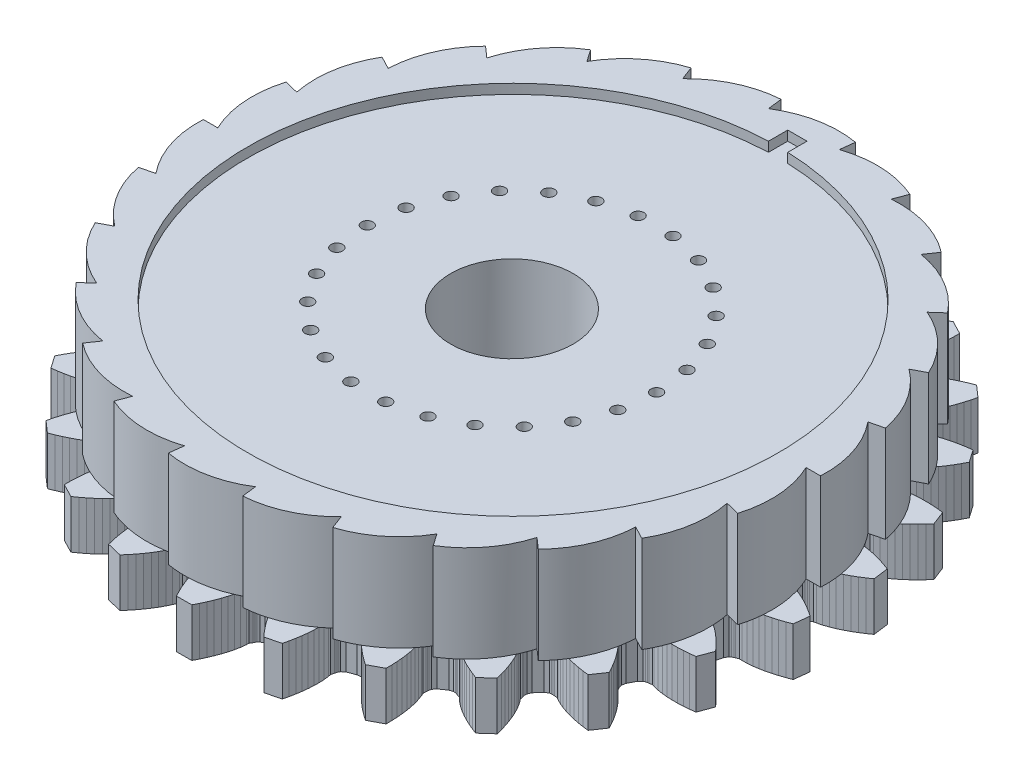
SolidWorks part; units mm, degrees
material "1060 Alloy"
ref_plane "Front Plane" through (0, 0, 0) normal (0, 0, 1) x (1, 0, 0)
ref_plane "Top Plane" through (0, 0, 0) normal (0, 1, 0) x (1, 0, 0)
ref_plane "Right Plane" through (0, 0, 0) normal (1, 0, 0) x (0, 0, -1)
sketch "Sketch1" plane through (0, 0, 0) normal (0, 1, 0) x (1, 0, 0)
  line L0 (0, 0) -> (54.8903, 0) construction
  line L1 (0, 0) -> (47.5263, 11.7142) construction
  line L2 (0, 0) -> (29.6137, 7.2991)
  line L3 (0, 0) -> (32, 0)
  circle A0 centre (0, 0) radius 32 construction
  circle A1 centre (0, 0) radius 30.5 construction
  arc A2 (29.6137, 7.2991) -> (32, 0) centre (21.3514, 0.5583) cw
  circle A3 centre (0, 0) radius 31.25 construction
  dimension "D1" = 62.5
  dimension "D2" = 1.5
  dimension "D4" = 0.75
  dimension "D3" = 13.846
extrude "Extrude ratchet edge" add sketch "Sketch1" along normal blind 10
pattern_circular "Pattern edge to form gear" count 26 over 360 about axis through (0, 0, 0) along (0, 1, 0) of "Extrude ratchet edge"
sketch "Sketch7" plane through (0, 10, 0) normal (0, 1, 0) x (1, 0, 0)
  circle A0 centre (0, 0) radius 6.35
  dimension "D1" = 12.7
sketch "Sketch12" plane through (0, 0, 0) normal (0, -1, 0) x (1, 0, 0)
  line L0 (29.0003, -0.6166) -> (29.1196, -1.0003)
  line L1 (29.1196, -1.0003) -> (29.244, -1.1506)
  line L2 (29.244, -1.1506) -> (29.3694, -1.2597)
  line L3 (29.3694, -1.2597) -> (29.4955, -1.346)
  line L4 (29.4955, -1.346) -> (29.7463, -1.5351)
  line L5 (29.7463, -1.5351) -> (30.0039, -1.5796)
  line L6 (30.0039, -1.5796) -> (30.5166, -1.7122)
  line L7 (30.5166, -1.7122) -> (31.0266, -1.8861)
  line L8 (31.0266, -1.8861) -> (31.5336, -2.0936)
  line L9 (31.5336, -2.0936) -> (32.0376, -2.3308)
  line L10 (32.0376, -2.3308) -> (32.5381, -2.595)
  line L11 (32.5381, -2.595) -> (33.035, -2.8848)
  line L12 (33.035, -2.8848) -> (33.5277, -3.1987)
  line L13 (33.5277, -3.1987) -> (34.0159, -3.5359)
  line L14 (34.0159, -3.5359) -> (33.8164, -5.1042)
  line L15 (33.8164, -5.1042) -> (33.2594, -5.3084)
  line L16 (33.2594, -5.3084) -> (32.7038, -5.4891)
  line L17 (32.7038, -5.4891) -> (32.1503, -5.6453)
  line L18 (32.1503, -5.6453) -> (31.5995, -5.7759)
  line L19 (31.5995, -5.7759) -> (31.0523, -5.8793)
  line L20 (31.0523, -5.8793) -> (30.5094, -5.9534)
  line L21 (30.5094, -5.9534) -> (29.9722, -5.9942)
  line L22 (29.9722, -5.9942) -> (29.4426, -5.9942)
  line L23 (29.4426, -5.9942) -> (29.182, -5.9728)
  line L24 (29.182, -5.9728) -> (28.8919, -6.0931)
  line L25 (28.8919, -6.0931) -> (28.7482, -6.1452)
  line L26 (28.7482, -6.1452) -> (28.5995, -6.2194)
  line L27 (28.5995, -6.2194) -> (28.4414, -6.3338)
  line L28 (28.4414, -6.3338) -> (28.2299, -6.6755)
  line L29 (28.2299, -6.6755) -> (28.0119, -7.539)
  line L30 (28.0119, -7.539) -> (28.0359, -7.9401)
  line L31 (28.0359, -7.9401) -> (28.1207, -8.1159)
  line L32 (28.1207, -8.1159) -> (28.2164, -8.2517)
  line L33 (28.2164, -8.2517) -> (28.3182, -8.3658)
  line L34 (28.3182, -8.3658) -> (28.5164, -8.6094)
  line L35 (28.5164, -8.6094) -> (28.7559, -8.7142)
  line L36 (28.7559, -8.7142) -> (29.222, -8.9657)
  line L37 (29.222, -8.9657) -> (29.6755, -9.2566)
  line L38 (29.6755, -9.2566) -> (30.1181, -9.5794)
  line L39 (30.1181, -9.5794) -> (30.5507, -9.9303)
  line L40 (30.5507, -9.9303) -> (30.9735, -10.3067)
  line L41 (30.9735, -10.3067) -> (31.3865, -10.7069)
  line L42 (31.3865, -10.7069) -> (31.7898, -11.1296)
  line L43 (31.7898, -11.1296) -> (32.1831, -11.5738)
  line L44 (32.1831, -11.5738) -> (31.6141, -13.0488)
  line L45 (31.6141, -13.0488) -> (31.0244, -13.1138)
  line L46 (31.0244, -13.1138) -> (30.4418, -13.1563)
  line L47 (30.4418, -13.1563) -> (29.8669, -13.1754)
  line L48 (29.8669, -13.1754) -> (29.3009, -13.1704)
  line L49 (29.3009, -13.1704) -> (28.7448, -13.1399)
  line L50 (28.7448, -13.1399) -> (28.2, -13.0819)
  line L51 (28.2, -13.0819) -> (27.6686, -12.9929)
  line L52 (27.6686, -12.9929) -> (27.1544, -12.8663)
  line L53 (27.1544, -12.8663) -> (26.9065, -12.7831)
  line L54 (26.9065, -12.7831) -> (26.5961, -12.8305)
  line L55 (26.5961, -12.8305) -> (26.4441, -12.8467)
  line L56 (26.4441, -12.8467) -> (26.2819, -12.8831)
  line L57 (26.2819, -12.8831) -> (26.1011, -12.9564)
  line L58 (26.1011, -12.9564) -> (25.814, -13.2375)
  line L59 (25.814, -13.2375) -> (25.3956, -14.0238)
  line L60 (25.3956, -14.0238) -> (25.3229, -14.4189)
  line L61 (25.3229, -14.4189) -> (25.3632, -14.6099)
  line L62 (25.3632, -14.6099) -> (25.4236, -14.7647)
  line L63 (25.4236, -14.7647) -> (25.4951, -14.8998)
  line L64 (25.4951, -14.8998) -> (25.6292, -15.1838)
  line L65 (25.6292, -15.1838) -> (25.8367, -15.3428)
  line L66 (25.8367, -15.3428) -> (26.2291, -15.6985)
  line L67 (26.2291, -15.6985) -> (26.5998, -16.0895)
  line L68 (26.5998, -16.0895) -> (26.9523, -16.5089)
  line L69 (26.9523, -16.5089) -> (27.2883, -16.9531)
  line L70 (27.2883, -16.9531) -> (27.6087, -17.4197)
  line L71 (27.6087, -17.4197) -> (27.914, -17.9072)
  line L72 (27.914, -17.9072) -> (28.2044, -18.4141)
  line L73 (28.2044, -18.4141) -> (28.48, -18.9395)
  line L74 (28.48, -18.9395) -> (27.5746, -20.2355)
  line L75 (27.5746, -20.2355) -> (26.9864, -20.1575)
  line L76 (26.9864, -20.1575) -> (26.4105, -20.0593)
  line L77 (26.4105, -20.0593) -> (25.8478, -19.9403)
  line L78 (25.8478, -19.9403) -> (25.2994, -19.8)
  line L79 (25.2994, -19.8) -> (24.7668, -19.6373)
  line L80 (24.7668, -19.6373) -> (24.2517, -19.4506)
  line L81 (24.2517, -19.4506) -> (23.7571, -19.237)
  line L82 (23.7571, -19.237) -> (23.2881, -18.991)
  line L83 (23.2881, -18.991) -> (23.0673, -18.8509)
  line L84 (23.0673, -18.8509) -> (22.7546, -18.8226)
  line L85 (22.7546, -18.8226) -> (22.6031, -18.802)
  line L86 (22.6031, -18.802) -> (22.4369, -18.7985)
  line L87 (22.4369, -18.7985) -> (22.2438, -18.8264)
  line L88 (22.2438, -18.8264) -> (21.8978, -19.0306)
  line L89 (21.8978, -19.0306) -> (21.3034, -19.694)
  line L90 (21.3034, -19.694) -> (21.1383, -20.0602)
  line L91 (21.1383, -20.0602) -> (21.1316, -20.2553)
  line L92 (21.1316, -20.2553) -> (21.1532, -20.4201)
  line L93 (21.1532, -20.4201) -> (21.1903, -20.5684)
  line L94 (21.1903, -20.5684) -> (21.2526, -20.8761)
  line L95 (21.2526, -20.8761) -> (21.416, -21.0803)
  line L96 (21.416, -21.0803) -> (21.7119, -21.5195)
  line L97 (21.7119, -21.5195) -> (21.9782, -21.9879)
  line L98 (21.9782, -21.9879) -> (22.2201, -22.4794)
  line L99 (22.2201, -22.4794) -> (22.4401, -22.9911)
  line L100 (22.4401, -22.9911) -> (22.6395, -23.5209)
  line L101 (22.6395, -23.5209) -> (22.8193, -24.0672)
  line L102 (22.8193, -24.0672) -> (22.9799, -24.6289)
  line L103 (22.9799, -24.6289) -> (23.1217, -25.205)
  line L104 (23.1217, -25.205) -> (21.9325, -26.2467)
  line L105 (21.9325, -26.2467) -> (21.3801, -26.0302)
  line L106 (21.3801, -26.0302) -> (20.8445, -25.797)
  line L107 (20.8445, -25.797) -> (20.3266, -25.5468)
  line L108 (20.3266, -25.5468) -> (19.8277, -25.2793)
  line L109 (19.8277, -25.2793) -> (19.3494, -24.9939)
  line L110 (19.3494, -24.9939) -> (18.894, -24.6893)
  line L111 (18.894, -24.6893) -> (18.4649, -24.3636)
  line L112 (18.4649, -24.3636) -> (18.0684, -24.0125)
  line L113 (18.0684, -24.0125) -> (17.8876, -23.8237)
  line L114 (17.8876, -23.8237) -> (17.5907, -23.7213)
  line L115 (17.5907, -23.7213) -> (17.4485, -23.665)
  line L116 (17.4485, -23.665) -> (17.288, -23.6219)
  line L117 (17.288, -23.6219) -> (17.0938, -23.6028)
  line L118 (17.0938, -23.6028) -> (16.709, -23.7182)
  line L119 (16.709, -23.7182) -> (15.9732, -24.22)
  line L120 (15.9732, -24.22) -> (15.7251, -24.5362)
  line L121 (15.7251, -24.5362) -> (15.672, -24.7239)
  line L122 (15.672, -24.7239) -> (15.6536, -24.8891)
  line L123 (15.6536, -24.8891) -> (15.6541, -25.042)
  line L124 (15.6541, -25.042) -> (15.641, -25.3558)
  line L125 (15.641, -25.3558) -> (15.7507, -25.593)
  line L126 (15.7507, -25.593) -> (15.9329, -26.0903)
  line L127 (15.9329, -26.0903) -> (16.0794, -26.6088)
  line L128 (16.0794, -26.6088) -> (16.1966, -27.144)
  line L129 (16.1966, -27.144) -> (16.2878, -27.6934)
  line L130 (16.2878, -27.6934) -> (16.3546, -28.2555)
  line L131 (16.3546, -28.2555) -> (16.3984, -28.829)
  line L132 (16.3984, -28.829) -> (16.4199, -29.4128)
  line L133 (16.4199, -29.4128) -> (16.4198, -30.0061)
  line L134 (16.4198, -30.0061) -> (15.0158, -30.7329)
  line L135 (15.0158, -30.7329) -> (14.5313, -30.3905)
  line L136 (14.5313, -30.3905) -> (14.067, -30.0359)
  line L137 (14.067, -30.0359) -> (13.624, -29.6691)
  line L138 (13.624, -29.6691) -> (13.2037, -29.29)
  line L139 (13.2037, -29.29) -> (12.8076, -28.8984)
  line L140 (12.8076, -28.8984) -> (12.4383, -28.4937)
  line L141 (12.4383, -28.4937) -> (12.0996, -28.0747)
  line L142 (12.0996, -28.0747) -> (11.7986, -27.6389)
  line L143 (11.7986, -27.6389) -> (11.6683, -27.4123)
  line L144 (11.6683, -27.4123) -> (11.4045, -27.2419)
  line L145 (11.4045, -27.2419) -> (11.28, -27.1532)
  line L146 (11.28, -27.1532) -> (11.1345, -27.0729)
  line L147 (11.1345, -27.0729) -> (10.9505, -27.0079)
  line L148 (10.9505, -27.0079) -> (10.5492, -27.0279)
  line L149 (10.5492, -27.0279) -> (9.7146, -27.339)
  line L150 (9.7146, -27.339) -> (9.3982, -27.5866)
  line L151 (9.3982, -27.5866) -> (9.3017, -27.7562)
  line L152 (9.3017, -27.7562) -> (9.2442, -27.9122)
  line L153 (9.2442, -27.9122) -> (9.2082, -28.0607)
  line L154 (9.2082, -28.0607) -> (9.1203, -28.3622)
  line L155 (9.1203, -28.3622) -> (9.1701, -28.6189)
  line L156 (9.1701, -28.6189) -> (9.2279, -29.1453)
  line L157 (9.2279, -29.1453) -> (9.2461, -29.6838)
  line L158 (9.2461, -29.6838) -> (9.2319, -30.2315)
  line L159 (9.2319, -30.2315) -> (9.1888, -30.7868)
  line L160 (9.1888, -30.7868) -> (9.1192, -31.3485)
  line L161 (9.1192, -31.3485) -> (9.0245, -31.9158)
  line L162 (9.0245, -31.9158) -> (8.9057, -32.4878)
  line L163 (8.9057, -32.4878) -> (8.7636, -33.0638)
  line L164 (8.7636, -33.0638) -> (7.2264, -33.4335)
  line L165 (7.2264, -33.4335) -> (6.8379, -32.9851)
  line L166 (6.8379, -32.9851) -> (6.472, -32.5297)
  line L167 (6.472, -32.5297) -> (6.1297, -32.0675)
  line L168 (6.1297, -32.0675) -> (5.8123, -31.5988)
  line L169 (5.8123, -31.5988) -> (5.5215, -31.1238)
  line L170 (5.5215, -31.1238) -> (5.2598, -30.6425)
  line L171 (5.2598, -30.6425) -> (5.0311, -30.1547)
  line L172 (5.0311, -30.1547) -> (4.8432, -29.6595)
  line L173 (4.8432, -29.6595) -> (4.7709, -29.4083)
  line L174 (4.7709, -29.4083) -> (4.5555, -29.1797)
  line L175 (4.5555, -29.1797) -> (4.4559, -29.0638)
  line L176 (4.4559, -29.0638) -> (4.3338, -28.951)
  line L177 (4.3338, -28.951) -> (4.1707, -28.8438)
  line L178 (4.1707, -28.8438) -> (3.7763, -28.7672)
  line L179 (3.7763, -28.7672) -> (2.8915, -28.8696)
  line L180 (2.8915, -28.8696) -> (2.525, -29.0342)
  line L181 (2.525, -29.0342) -> (2.3907, -29.1758)
  line L182 (2.3907, -29.1758) -> (2.2976, -29.3135)
  line L183 (2.2976, -29.3135) -> (2.2271, -29.4491)
  line L184 (2.2271, -29.4491) -> (2.0696, -29.7208)
  line L185 (2.0696, -29.7208) -> (2.0565, -29.9819)
  line L186 (2.0565, -29.9819) -> (1.9867, -30.5069)
  line L187 (1.9867, -30.5069) -> (1.8755, -31.0341)
  line L188 (1.8755, -31.0341) -> (1.7306, -31.5624)
  line L189 (1.7306, -31.5624) -> (1.5559, -32.0913)
  line L190 (1.5559, -32.0913) -> (1.3539, -32.6201)
  line L191 (1.3539, -32.6201) -> (1.1262, -33.1482)
  line L192 (1.1262, -33.1482) -> (0.8739, -33.6752)
  line L193 (0.8739, -33.6752) -> (0.5981, -34.2004)
  line L194 (0.5981, -34.2004) -> (-0.9829, -34.1915)
  line L195 (-0.9829, -34.1915) -> (-1.2528, -33.6632)
  line L196 (-1.2528, -33.6632) -> (-1.499, -33.1334)
  line L197 (-1.499, -33.1334) -> (-1.7208, -32.6027)
  line L198 (-1.7208, -32.6027) -> (-1.9169, -32.0717)
  line L199 (-1.9169, -32.0717) -> (-2.0855, -31.5409)
  line L200 (-2.0855, -31.5409) -> (-2.2244, -31.011)
  line L201 (-2.2244, -31.011) -> (-2.3297, -30.4826)
  line L202 (-2.3297, -30.4826) -> (-2.3936, -29.9568)
  line L203 (-2.3936, -29.9568) -> (-2.4037, -29.6956)
  line L204 (-2.4037, -29.6956) -> (-2.5581, -29.4221)
  line L205 (-2.5581, -29.4221) -> (-2.6272, -29.2857)
  line L206 (-2.6272, -29.2857) -> (-2.7187, -29.147)
  line L207 (-2.7187, -29.147) -> (-2.8514, -29.0039)
  line L208 (-2.8514, -29.0039) -> (-3.216, -28.8351)
  line L209 (-3.216, -28.8351) -> (-4.0996, -28.7228)
  line L210 (-4.0996, -28.7228) -> (-4.4948, -28.7949)
  line L211 (-4.4948, -28.7949) -> (-4.6591, -28.9003)
  line L212 (-4.6591, -28.9003) -> (-4.7824, -29.0117)
  line L213 (-4.7824, -29.0117) -> (-4.8834, -29.1265)
  line L214 (-4.8834, -29.1265) -> (-5.1013, -29.3526)
  line L215 (-5.1013, -29.3526) -> (-5.1765, -29.603)
  line L216 (-5.1765, -29.603) -> (-5.37, -30.096)
  line L217 (-5.37, -30.096) -> (-5.6041, -30.5812)
  line L218 (-5.6041, -30.5812) -> (-5.8712, -31.0596)
  line L219 (-5.8712, -31.0596) -> (-6.1674, -31.5313)
  line L220 (-6.1674, -31.5313) -> (-6.4901, -31.9963)
  line L221 (-6.4901, -31.9963) -> (-6.8376, -32.4546)
  line L222 (-6.8376, -32.4546) -> (-7.2086, -32.9059)
  line L223 (-7.2086, -32.9059) -> (-7.6021, -33.3499)
  line L224 (-7.6021, -33.3499) -> (-9.135, -32.9629)
  line L225 (-9.135, -32.9629) -> (-9.2706, -32.3853)
  line L226 (-9.2706, -32.3853) -> (-9.383, -31.812)
  line L227 (-9.383, -31.812) -> (-9.4713, -31.2437)
  line L228 (-9.4713, -31.2437) -> (-9.5346, -30.6812)
  line L229 (-9.5346, -30.6812) -> (-9.5713, -30.1254)
  line L230 (-9.5713, -30.1254) -> (-9.5793, -29.5776)
  line L231 (-9.5793, -29.5776) -> (-9.5551, -29.0394)
  line L232 (-9.5551, -29.0394) -> (-9.4913, -28.5136)
  line L233 (-9.4913, -28.5136) -> (-9.4387, -28.2576)
  line L234 (-9.4387, -28.2576) -> (-9.5231, -27.9551)
  line L235 (-9.5231, -27.9551) -> (-9.5575, -27.8061)
  line L236 (-9.5575, -27.8061) -> (-9.6132, -27.6496)
  line L237 (-9.6132, -27.6496) -> (-9.7078, -27.4789)
  line L238 (-9.7078, -27.4789) -> (-10.0214, -27.2277)
  line L239 (-10.0214, -27.2277) -> (-10.8524, -26.9072)
  line L240 (-10.8524, -26.9072) -> (-11.2535, -26.8827)
  line L241 (-11.2535, -26.8827) -> (-11.4382, -26.9456)
  line L242 (-11.4382, -26.9456) -> (-11.5846, -27.0243)
  line L243 (-11.5846, -27.0243) -> (-11.7101, -27.1116)
  line L244 (-11.7101, -27.1116) -> (-11.9758, -27.279)
  line L245 (-11.9758, -27.279) -> (-12.1087, -27.5041)
  line L246 (-12.1087, -27.5041) -> (-12.4145, -27.9365)
  line L247 (-12.4145, -27.9365) -> (-12.758, -28.3516)
  line L248 (-12.758, -28.3516) -> (-13.1318, -28.7521)
  line L249 (-13.1318, -28.7521) -> (-13.5322, -29.1392)
  line L250 (-13.5322, -29.1392) -> (-13.9568, -29.5135)
  line L251 (-13.9568, -29.5135) -> (-14.4039, -29.8753)
  line L252 (-14.4039, -29.8753) -> (-14.8722, -30.2247)
  line L253 (-14.8722, -30.2247) -> (-15.3605, -30.5616)
  line L254 (-15.3605, -30.5616) -> (-16.7562, -29.819)
  line L255 (-16.7562, -29.819) -> (-16.7497, -29.2258)
  line L256 (-16.7497, -29.2258) -> (-16.7216, -28.6422)
  line L257 (-16.7216, -28.6422) -> (-16.6713, -28.0693)
  line L258 (-16.6713, -28.0693) -> (-16.5981, -27.508)
  line L259 (-16.5981, -27.508) -> (-16.5008, -26.9596)
  line L260 (-16.5008, -26.9596) -> (-16.3775, -26.4258)
  line L261 (-16.3775, -26.4258) -> (-16.2252, -25.909)
  line L262 (-16.2252, -25.909) -> (-16.0374, -25.4138)
  line L263 (-16.0374, -25.4138) -> (-15.925, -25.1778)
  line L264 (-15.925, -25.1778) -> (-15.9346, -24.8639)
  line L265 (-15.9346, -24.8639) -> (-15.9324, -24.711)
  line L266 (-15.9324, -24.711) -> (-15.949, -24.5456)
  line L267 (-15.949, -24.5456) -> (-15.9999, -24.3573)
  line L268 (-15.9999, -24.3573) -> (-16.2444, -24.0384)
  line L269 (-16.2444, -24.0384) -> (-16.9745, -23.5283)
  line L270 (-16.9745, -23.5283) -> (-17.358, -23.4085)
  line L271 (-17.358, -23.4085) -> (-17.5524, -23.4254)
  line L272 (-17.5524, -23.4254) -> (-17.7134, -23.4668)
  line L273 (-17.7134, -23.4668) -> (-17.8562, -23.5215)
  line L274 (-17.8562, -23.5215) -> (-18.1542, -23.6204)
  line L275 (-18.1542, -23.6204) -> (-18.3371, -23.8072)
  line L276 (-18.3371, -23.8072) -> (-18.7375, -24.1538)
  line L277 (-18.7375, -24.1538) -> (-19.1704, -24.4747)
  line L278 (-19.1704, -24.4747) -> (-19.6292, -24.7741)
  line L279 (-19.6292, -24.7741) -> (-20.1106, -25.0541)
  line L280 (-20.1106, -25.0541) -> (-20.6125, -25.316)
  line L281 (-20.6125, -25.316) -> (-21.1332, -25.5603)
  line L282 (-21.1332, -25.5603) -> (-21.6714, -25.7874)
  line L283 (-21.6714, -25.7874) -> (-22.2262, -25.9977)
  line L284 (-22.2262, -25.9977) -> (-23.4036, -24.9426)
  line L285 (-23.4036, -24.9426) -> (-23.2553, -24.3682)
  line L286 (-23.2553, -24.3682) -> (-23.0883, -23.8083)
  line L287 (-23.0883, -23.8083) -> (-22.9024, -23.2641)
  line L288 (-22.9024, -23.2641) -> (-22.6971, -22.7366)
  line L289 (-22.6971, -22.7366) -> (-22.4713, -22.2274)
  line L290 (-22.4713, -22.2274) -> (-22.2239, -21.7386)
  line L291 (-22.2239, -21.7386) -> (-21.9523, -21.2733)
  line L292 (-21.9523, -21.2733) -> (-21.6515, -20.8374)
  line L293 (-21.6515, -20.8374) -> (-21.4858, -20.6352)
  line L294 (-21.4858, -20.6352) -> (-21.4201, -20.3281)
  line L295 (-21.4201, -20.3281) -> (-21.3813, -20.1802)
  line L296 (-21.3813, -20.1802) -> (-21.3578, -20.0157)
  line L297 (-21.3578, -20.0157) -> (-21.3622, -19.8206)
  line L298 (-21.3622, -19.8206) -> (-21.5232, -19.4525)
  line L299 (-21.5232, -19.4525) -> (-22.1101, -18.7825)
  line L300 (-22.1101, -18.7825) -> (-22.4538, -18.5744)
  line L301 (-22.4538, -18.5744) -> (-22.6466, -18.5443)
  line L302 (-22.6466, -18.5443) -> (-22.8128, -18.5459)
  line L303 (-22.8128, -18.5459) -> (-22.9645, -18.5648)
  line L304 (-22.9645, -18.5648) -> (-23.2775, -18.5896)
  line L305 (-23.2775, -18.5896) -> (-23.4999, -18.7272)
  line L306 (-23.4999, -18.7272) -> (-23.9716, -18.9679)
  line L307 (-23.9716, -18.9679) -> (-24.4686, -19.1758)
  line L308 (-24.4686, -19.1758) -> (-24.9858, -19.3568)
  line L309 (-24.9858, -19.3568) -> (-25.5202, -19.5135)
  line L310 (-25.5202, -19.5135) -> (-26.0702, -19.6476)
  line L311 (-26.0702, -19.6476) -> (-26.6342, -19.7602)
  line L312 (-26.6342, -19.7602) -> (-27.2111, -19.8519)
  line L313 (-27.2111, -19.8519) -> (-27.8001, -19.9233)
  line L314 (-27.8001, -19.9233) -> (-28.6909, -18.6171)
  line L315 (-28.6909, -18.6171) -> (-28.4094, -18.0949)
  line L316 (-28.4094, -18.0949) -> (-28.1133, -17.5912)
  line L317 (-28.1133, -17.5912) -> (-27.8025, -17.1073)
  line L318 (-27.8025, -17.1073) -> (-27.4769, -16.6443)
  line L319 (-27.4769, -16.6443) -> (-27.1359, -16.2039)
  line L320 (-27.1359, -16.2039) -> (-26.7786, -15.7885)
  line L321 (-26.7786, -15.7885) -> (-26.4036, -15.4018)
  line L322 (-26.4036, -15.4018) -> (-26.0072, -15.0505)
  line L323 (-26.0072, -15.0505) -> (-25.7979, -14.8938)
  line L324 (-25.7979, -14.8938) -> (-25.6606, -14.6114)
  line L325 (-25.6606, -14.6114) -> (-25.5876, -14.4771)
  line L326 (-25.5876, -14.4771) -> (-25.5254, -14.3229)
  line L327 (-25.5254, -14.3229) -> (-25.483, -14.1325)
  line L328 (-25.483, -14.1325) -> (-25.5512, -13.7365)
  line L329 (-25.5512, -13.7365) -> (-25.9607, -12.9455)
  line L330 (-25.9607, -12.9455) -> (-26.2446, -12.6612)
  line L331 (-26.2446, -12.6612) -> (-26.4246, -12.5859)
  line L332 (-26.4246, -12.5859) -> (-26.5864, -12.5476)
  line L333 (-26.5864, -12.5476) -> (-26.7382, -12.5297)
  line L334 (-26.7382, -12.5297) -> (-27.0481, -12.4789)
  line L335 (-27.0481, -12.4789) -> (-27.2968, -12.5592)
  line L336 (-27.2968, -12.5592) -> (-27.8125, -12.6801)
  line L337 (-27.8125, -12.6801) -> (-28.3448, -12.763)
  line L338 (-28.3448, -12.763) -> (-28.8902, -12.8149)
  line L339 (-28.8902, -12.8149) -> (-29.4467, -12.8392)
  line L340 (-29.4467, -12.8392) -> (-30.0127, -12.8378)
  line L341 (-30.0127, -12.8378) -> (-30.5873, -12.8121)
  line L342 (-30.5873, -12.8121) -> (-31.1694, -12.7631)
  line L343 (-31.1694, -12.7631) -> (-31.7584, -12.6915)
  line L344 (-31.7584, -12.6915) -> (-32.3107, -11.2101)
  line L345 (-32.3107, -11.2101) -> (-31.9124, -10.7704)
  line L346 (-31.9124, -10.7704) -> (-31.5044, -10.3522)
  line L347 (-31.5044, -10.3522) -> (-31.0868, -9.9567)
  line L348 (-31.0868, -9.9567) -> (-30.6598, -9.5851)
  line L349 (-30.6598, -9.5851) -> (-30.2233, -9.2392)
  line L350 (-30.2233, -9.2392) -> (-29.7771, -8.9214)
  line L351 (-29.7771, -8.9214) -> (-29.3203, -8.6356)
  line L352 (-29.3203, -8.6356) -> (-28.8514, -8.3894)
  line L353 (-28.8514, -8.3894) -> (-28.6108, -8.2873)
  line L354 (-28.6108, -8.2873) -> (-28.4098, -8.0459)
  line L355 (-28.4098, -8.0459) -> (-28.3068, -7.933)
  line L356 (-28.3068, -7.933) -> (-28.2095, -7.7982)
  line L357 (-28.2095, -7.7982) -> (-28.1228, -7.6234)
  line L358 (-28.1228, -7.6234) -> (-28.0943, -7.2226)
  line L359 (-28.0943, -7.2226) -> (-28.3025, -6.3567)
  line L360 (-28.3025, -6.3567) -> (-28.5102, -6.0127)
  line L361 (-28.5102, -6.0127) -> (-28.6669, -5.8964)
  line L362 (-28.6669, -5.8964) -> (-28.8148, -5.8206)
  line L363 (-28.8148, -5.8206) -> (-28.9579, -5.7669)
  line L364 (-28.9579, -5.7669) -> (-29.2466, -5.6433)
  line L365 (-29.2466, -5.6433) -> (-29.5074, -5.6618)
  line L366 (-29.5074, -5.6618) -> (-30.037, -5.6558)
  line L367 (-30.037, -5.6558) -> (-30.5737, -5.6089)
  line L368 (-30.5737, -5.6089) -> (-31.1157, -5.5288)
  line L369 (-31.1157, -5.5288) -> (-31.6618, -5.4192)
  line L370 (-31.6618, -5.4192) -> (-32.211, -5.2824)
  line L371 (-32.211, -5.2824) -> (-32.7628, -5.1199)
  line L372 (-32.7628, -5.1199) -> (-33.3163, -4.933)
  line L373 (-33.3163, -4.933) -> (-33.871, -4.7225)
  line L374 (-33.871, -4.7225) -> (-34.0527, -3.152)
  line L375 (-34.0527, -3.152) -> (-33.5607, -2.8204)
  line L376 (-33.5607, -2.8204) -> (-33.0645, -2.5121)
  line L377 (-33.0645, -2.5121) -> (-32.5644, -2.228)
  line L378 (-32.5644, -2.228) -> (-32.0609, -1.9693)
  line L379 (-32.0609, -1.9693) -> (-31.5543, -1.7379)
  line L380 (-31.5543, -1.7379) -> (-31.045, -1.5361)
  line L381 (-31.045, -1.5361) -> (-30.5331, -1.3679)
  line L382 (-30.5331, -1.3679) -> (-30.0189, -1.2411)
  line L383 (-30.0189, -1.2411) -> (-29.7608, -1.1996)
  line L384 (-29.7608, -1.1996) -> (-29.5079, -1.0133)
  line L385 (-29.5079, -1.0133) -> (-29.3809, -0.9284)
  line L386 (-29.3809, -0.9284) -> (-29.2542, -0.8208)
  line L387 (-29.2542, -0.8208) -> (-29.1281, -0.6718)
  line L388 (-29.1281, -0.6718) -> (-29.0045, -0.2895)
  line L389 (-29.0045, -0.2895) -> (-28.9995, 0.6011)
  line L390 (-28.9995, 0.6011) -> (-29.1188, 0.9848)
  line L391 (-29.1188, 0.9848) -> (-29.2432, 1.1352)
  line L392 (-29.2432, 1.1352) -> (-29.3686, 1.2442)
  line L393 (-29.3686, 1.2442) -> (-29.4947, 1.3306)
  line L394 (-29.4947, 1.3306) -> (-29.7455, 1.5197)
  line L395 (-29.7455, 1.5197) -> (-30.0031, 1.5641)
  line L396 (-30.0031, 1.5641) -> (-30.5158, 1.6968)
  line L397 (-30.5158, 1.6968) -> (-31.0257, 1.8707)
  line L398 (-31.0257, 1.8707) -> (-31.5328, 2.0782)
  line L399 (-31.5328, 2.0782) -> (-32.0368, 2.3153)
  line L400 (-32.0368, 2.3153) -> (-32.5373, 2.5796)
  line L401 (-32.5373, 2.5796) -> (-33.0342, 2.8694)
  line L402 (-33.0342, 2.8694) -> (-33.5269, 3.1833)
  line L403 (-33.5269, 3.1833) -> (-34.0151, 3.5204)
  line L404 (-34.0151, 3.5204) -> (-33.8156, 5.0888)
  line L405 (-33.8156, 5.0888) -> (-33.2586, 5.293)
  line L406 (-33.2586, 5.293) -> (-32.703, 5.4737)
  line L407 (-32.703, 5.4737) -> (-32.1495, 5.6298)
  line L408 (-32.1495, 5.6298) -> (-31.5987, 5.7604)
  line L409 (-31.5987, 5.7604) -> (-31.0515, 5.8639)
  line L410 (-31.0515, 5.8639) -> (-30.5086, 5.9379)
  line L411 (-30.5086, 5.9379) -> (-29.9714, 5.9787)
  line L412 (-29.9714, 5.9787) -> (-29.4418, 5.9788)
  line L413 (-29.4418, 5.9788) -> (-29.1812, 5.9574)
  line L414 (-29.1812, 5.9574) -> (-28.8911, 6.0777)
  line L415 (-28.8911, 6.0777) -> (-28.7474, 6.1298)
  line L416 (-28.7474, 6.1298) -> (-28.5987, 6.2039)
  line L417 (-28.5987, 6.2039) -> (-28.4406, 6.3184)
  line L418 (-28.4406, 6.3184) -> (-28.2291, 6.66)
  line L419 (-28.2291, 6.66) -> (-28.0111, 7.5236)
  line L420 (-28.0111, 7.5236) -> (-28.0351, 7.9247)
  line L421 (-28.0351, 7.9247) -> (-28.1199, 8.1004)
  line L422 (-28.1199, 8.1004) -> (-28.2156, 8.2363)
  line L423 (-28.2156, 8.2363) -> (-28.3174, 8.3504)
  line L424 (-28.3174, 8.3504) -> (-28.5156, 8.594)
  line L425 (-28.5156, 8.594) -> (-28.7551, 8.6988)
  line L426 (-28.7551, 8.6988) -> (-29.2212, 8.9502)
  line L427 (-29.2212, 8.9502) -> (-29.6746, 9.2412)
  line L428 (-29.6746, 9.2412) -> (-30.1173, 9.564)
  line L429 (-30.1173, 9.564) -> (-30.5499, 9.9148)
  line L430 (-30.5499, 9.9148) -> (-30.9727, 10.2912)
  line L431 (-30.9727, 10.2912) -> (-31.3857, 10.6914)
  line L432 (-31.3857, 10.6914) -> (-31.789, 11.1142)
  line L433 (-31.789, 11.1142) -> (-32.1823, 11.5583)
  line L434 (-32.1823, 11.5583) -> (-31.6133, 13.0334)
  line L435 (-31.6133, 13.0334) -> (-31.0236, 13.0984)
  line L436 (-31.0236, 13.0984) -> (-30.4409, 13.1408)
  line L437 (-30.4409, 13.1408) -> (-29.8661, 13.16)
  line L438 (-29.8661, 13.16) -> (-29.3001, 13.155)
  line L439 (-29.3001, 13.155) -> (-28.744, 13.1245)
  line L440 (-28.744, 13.1245) -> (-28.1992, 13.0665)
  line L441 (-28.1992, 13.0665) -> (-27.6678, 12.9775)
  line L442 (-27.6678, 12.9775) -> (-27.1536, 12.8508)
  line L443 (-27.1536, 12.8508) -> (-26.9057, 12.7677)
  line L444 (-26.9057, 12.7677) -> (-26.5953, 12.8151)
  line L445 (-26.5953, 12.8151) -> (-26.4433, 12.8312)
  line L446 (-26.4433, 12.8312) -> (-26.2811, 12.8676)
  line L447 (-26.2811, 12.8676) -> (-26.1002, 12.941)
  line L448 (-26.1002, 12.941) -> (-25.8131, 13.222)
  line L449 (-25.8131, 13.222) -> (-25.3948, 14.0083)
  line L450 (-25.3948, 14.0083) -> (-25.3221, 14.4035)
  line L451 (-25.3221, 14.4035) -> (-25.3623, 14.5945)
  line L452 (-25.3623, 14.5945) -> (-25.4228, 14.7493)
  line L453 (-25.4228, 14.7493) -> (-25.4943, 14.8844)
  line L454 (-25.4943, 14.8844) -> (-25.6284, 15.1683)
  line L455 (-25.6284, 15.1683) -> (-25.8359, 15.3274)
  line L456 (-25.8359, 15.3274) -> (-26.2283, 15.6831)
  line L457 (-26.2283, 15.6831) -> (-26.5989, 16.0741)
  line L458 (-26.5989, 16.0741) -> (-26.9515, 16.4935)
  line L459 (-26.9515, 16.4935) -> (-27.2875, 16.9377)
  line L460 (-27.2875, 16.9377) -> (-27.6079, 17.4043)
  line L461 (-27.6079, 17.4043) -> (-27.9132, 17.8917)
  line L462 (-27.9132, 17.8917) -> (-28.2036, 18.3987)
  line L463 (-28.2036, 18.3987) -> (-28.4792, 18.9241)
  line L464 (-28.4792, 18.9241) -> (-27.5738, 20.2201)
  line L465 (-27.5738, 20.2201) -> (-26.9856, 20.1421)
  line L466 (-26.9856, 20.1421) -> (-26.4097, 20.0438)
  line L467 (-26.4097, 20.0438) -> (-25.847, 19.9249)
  line L468 (-25.847, 19.9249) -> (-25.2986, 19.7846)
  line L469 (-25.2986, 19.7846) -> (-24.766, 19.6219)
  line L470 (-24.766, 19.6219) -> (-24.2509, 19.4351)
  line L471 (-24.2509, 19.4351) -> (-23.7562, 19.2216)
  line L472 (-23.7562, 19.2216) -> (-23.2873, 18.9756)
  line L473 (-23.2873, 18.9756) -> (-23.0665, 18.8355)
  line L474 (-23.0665, 18.8355) -> (-22.7538, 18.8072)
  line L475 (-22.7538, 18.8072) -> (-22.6023, 18.7865)
  line L476 (-22.6023, 18.7865) -> (-22.4361, 18.7831)
  line L477 (-22.4361, 18.7831) -> (-22.243, 18.811)
  line L478 (-22.243, 18.811) -> (-21.897, 19.0152)
  line L479 (-21.897, 19.0152) -> (-21.3026, 19.6785)
  line L480 (-21.3026, 19.6785) -> (-21.1374, 20.0448)
  line L481 (-21.1374, 20.0448) -> (-21.1308, 20.2399)
  line L482 (-21.1308, 20.2399) -> (-21.1524, 20.4046)
  line L483 (-21.1524, 20.4046) -> (-21.1895, 20.5529)
  line L484 (-21.1895, 20.5529) -> (-21.2518, 20.8607)
  line L485 (-21.2518, 20.8607) -> (-21.4152, 21.0648)
  line L486 (-21.4152, 21.0648) -> (-21.7111, 21.5041)
  line L487 (-21.7111, 21.5041) -> (-21.9774, 21.9724)
  line L488 (-21.9774, 21.9724) -> (-22.2193, 22.464)
  line L489 (-22.2193, 22.464) -> (-22.4393, 22.9757)
  line L490 (-22.4393, 22.9757) -> (-22.6387, 23.5054)
  line L491 (-22.6387, 23.5054) -> (-22.8185, 24.0518)
  line L492 (-22.8185, 24.0518) -> (-22.9791, 24.6135)
  line L493 (-22.9791, 24.6135) -> (-23.1209, 25.1896)
  line L494 (-23.1209, 25.1896) -> (-21.9317, 26.2312)
  line L495 (-21.9317, 26.2312) -> (-21.3793, 26.0148)
  line L496 (-21.3793, 26.0148) -> (-20.8436, 25.7815)
  line L497 (-20.8436, 25.7815) -> (-20.3258, 25.5314)
  line L498 (-20.3258, 25.5314) -> (-19.8269, 25.2639)
  line L499 (-19.8269, 25.2639) -> (-19.3486, 24.9785)
  line L500 (-19.3486, 24.9785) -> (-18.8932, 24.6739)
  line L501 (-18.8932, 24.6739) -> (-18.464, 24.3482)
  line L502 (-18.464, 24.3482) -> (-18.0676, 23.997)
  line L503 (-18.0676, 23.997) -> (-17.8868, 23.8082)
  line L504 (-17.8868, 23.8082) -> (-17.5899, 23.7059)
  line L505 (-17.5899, 23.7059) -> (-17.4477, 23.6496)
  line L506 (-17.4477, 23.6496) -> (-17.2872, 23.6065)
  line L507 (-17.2872, 23.6065) -> (-17.093, 23.5873)
  line L508 (-17.093, 23.5873) -> (-16.7082, 23.7028)
  line L509 (-16.7082, 23.7028) -> (-15.9723, 24.2046)
  line L510 (-15.9723, 24.2046) -> (-15.7243, 24.5207)
  line L511 (-15.7243, 24.5207) -> (-15.6712, 24.7085)
  line L512 (-15.6712, 24.7085) -> (-15.6528, 24.8737)
  line L513 (-15.6528, 24.8737) -> (-15.6533, 25.0266)
  line L514 (-15.6533, 25.0266) -> (-15.6401, 25.3403)
  line L515 (-15.6401, 25.3403) -> (-15.7499, 25.5776)
  line L516 (-15.7499, 25.5776) -> (-15.932, 26.0749)
  line L517 (-15.932, 26.0749) -> (-16.0786, 26.5934)
  line L518 (-16.0786, 26.5934) -> (-16.1958, 27.1285)
  line L519 (-16.1958, 27.1285) -> (-16.2869, 27.678)
  line L520 (-16.2869, 27.678) -> (-16.3538, 28.2401)
  line L521 (-16.3538, 28.2401) -> (-16.3976, 28.8136)
  line L522 (-16.3976, 28.8136) -> (-16.4191, 29.3974)
  line L523 (-16.4191, 29.3974) -> (-16.419, 29.9907)
  line L524 (-16.419, 29.9907) -> (-15.015, 30.7175)
  line L525 (-15.015, 30.7175) -> (-14.5305, 30.3751)
  line L526 (-14.5305, 30.3751) -> (-14.0662, 30.0205)
  line L527 (-14.0662, 30.0205) -> (-13.6232, 29.6536)
  line L528 (-13.6232, 29.6536) -> (-13.2028, 29.2746)
  line L529 (-13.2028, 29.2746) -> (-12.8068, 28.8829)
  line L530 (-12.8068, 28.8829) -> (-12.4375, 28.4782)
  line L531 (-12.4375, 28.4782) -> (-12.0988, 28.0593)
  line L532 (-12.0988, 28.0593) -> (-11.7978, 27.6235)
  line L533 (-11.7978, 27.6235) -> (-11.6675, 27.3969)
  line L534 (-11.6675, 27.3969) -> (-11.4037, 27.2265)
  line L535 (-11.4037, 27.2265) -> (-11.2792, 27.1378)
  line L536 (-11.2792, 27.1378) -> (-11.1336, 27.0575)
  line L537 (-11.1336, 27.0575) -> (-10.9497, 26.9924)
  line L538 (-10.9497, 26.9924) -> (-10.5484, 27.0125)
  line L539 (-10.5484, 27.0125) -> (-9.7138, 27.3236)
  line L540 (-9.7138, 27.3236) -> (-9.3974, 27.5712)
  line L541 (-9.3974, 27.5712) -> (-9.3009, 27.7408)
  line L542 (-9.3009, 27.7408) -> (-9.2434, 27.8967)
  line L543 (-9.2434, 27.8967) -> (-9.2073, 28.0453)
  line L544 (-9.2073, 28.0453) -> (-9.1195, 28.3468)
  line L545 (-9.1195, 28.3468) -> (-9.1693, 28.6034)
  line L546 (-9.1693, 28.6034) -> (-9.2271, 29.1299)
  line L547 (-9.2271, 29.1299) -> (-9.2453, 29.6683)
  line L548 (-9.2453, 29.6683) -> (-9.231, 30.216)
  line L549 (-9.231, 30.216) -> (-9.188, 30.7713)
  line L550 (-9.188, 30.7713) -> (-9.1184, 31.3331)
  line L551 (-9.1184, 31.3331) -> (-9.0237, 31.9004)
  line L552 (-9.0237, 31.9004) -> (-8.9049, 32.4724)
  line L553 (-8.9049, 32.4724) -> (-8.7628, 33.0484)
  line L554 (-8.7628, 33.0484) -> (-7.2256, 33.4181)
  line L555 (-7.2256, 33.4181) -> (-6.8371, 32.9697)
  line L556 (-6.8371, 32.9697) -> (-6.4712, 32.5142)
  line L557 (-6.4712, 32.5142) -> (-6.1289, 32.0521)
  line L558 (-6.1289, 32.0521) -> (-5.8115, 31.5834)
  line L559 (-5.8115, 31.5834) -> (-5.5207, 31.1084)
  line L560 (-5.5207, 31.1084) -> (-5.259, 30.6271)
  line L561 (-5.259, 30.6271) -> (-5.0303, 30.1392)
  line L562 (-5.0303, 30.1392) -> (-4.8424, 29.644)
  line L563 (-4.8424, 29.644) -> (-4.7701, 29.3928)
  line L564 (-4.7701, 29.3928) -> (-4.5547, 29.1643)
  line L565 (-4.5547, 29.1643) -> (-4.4551, 29.0483)
  line L566 (-4.4551, 29.0483) -> (-4.333, 28.9356)
  line L567 (-4.333, 28.9356) -> (-4.1699, 28.8284)
  line L568 (-4.1699, 28.8284) -> (-3.7755, 28.7518)
  line L569 (-3.7755, 28.7518) -> (-2.8907, 28.8541)
  line L570 (-2.8907, 28.8541) -> (-2.5242, 29.0188)
  line L571 (-2.5242, 29.0188) -> (-2.3899, 29.1604)
  line L572 (-2.3899, 29.1604) -> (-2.2968, 29.2981)
  line L573 (-2.2968, 29.2981) -> (-2.2263, 29.4337)
  line L574 (-2.2263, 29.4337) -> (-2.0688, 29.7054)
  line L575 (-2.0688, 29.7054) -> (-2.0557, 29.9665)
  line L576 (-2.0557, 29.9665) -> (-1.9859, 30.4915)
  line L577 (-1.9859, 30.4915) -> (-1.8747, 31.0186)
  line L578 (-1.8747, 31.0186) -> (-1.7298, 31.547)
  line L579 (-1.7298, 31.547) -> (-1.5551, 32.0759)
  line L580 (-1.5551, 32.0759) -> (-1.3531, 32.6047)
  line L581 (-1.3531, 32.6047) -> (-1.1254, 33.1328)
  line L582 (-1.1254, 33.1328) -> (-0.8731, 33.6597)
  line L583 (-0.8731, 33.6597) -> (-0.5973, 34.185)
  line L584 (-0.5973, 34.185) -> (0.9837, 34.1761)
  line L585 (0.9837, 34.1761) -> (1.2536, 33.6477)
  line L586 (1.2536, 33.6477) -> (1.4999, 33.118)
  line L587 (1.4999, 33.118) -> (1.7216, 32.5873)
  line L588 (1.7216, 32.5873) -> (1.9177, 32.0563)
  line L589 (1.9177, 32.0563) -> (2.0863, 31.5255)
  line L590 (2.0863, 31.5255) -> (2.2252, 30.9955)
  line L591 (2.2252, 30.9955) -> (2.3305, 30.4671)
  line L592 (2.3305, 30.4671) -> (2.3944, 29.9414)
  line L593 (2.3944, 29.9414) -> (2.4046, 29.6802)
  line L594 (2.4046, 29.6802) -> (2.5589, 29.4067)
  line L595 (2.5589, 29.4067) -> (2.628, 29.2703)
  line L596 (2.628, 29.2703) -> (2.7195, 29.1316)
  line L597 (2.7195, 29.1316) -> (2.8522, 28.9885)
  line L598 (2.8522, 28.9885) -> (3.2168, 28.8197)
  line L599 (3.2168, 28.8197) -> (4.1004, 28.7074)
  line L600 (4.1004, 28.7074) -> (4.4956, 28.7795)
  line L601 (4.4956, 28.7795) -> (4.6599, 28.8849)
  line L602 (4.6599, 28.8849) -> (4.7833, 28.9963)
  line L603 (4.7833, 28.9963) -> (4.8842, 29.111)
  line L604 (4.8842, 29.111) -> (5.1021, 29.3372)
  line L605 (5.1021, 29.3372) -> (5.1773, 29.5876)
  line L606 (5.1773, 29.5876) -> (5.3708, 30.0806)
  line L607 (5.3708, 30.0806) -> (5.6049, 30.5658)
  line L608 (5.6049, 30.5658) -> (5.872, 31.0441)
  line L609 (5.872, 31.0441) -> (6.1682, 31.5159)
  line L610 (6.1682, 31.5159) -> (6.4909, 31.9809)
  line L611 (6.4909, 31.9809) -> (6.8384, 32.4392)
  line L612 (6.8384, 32.4392) -> (7.2094, 32.8905)
  line L613 (7.2094, 32.8905) -> (7.6029, 33.3345)
  line L614 (7.6029, 33.3345) -> (9.1358, 32.9475)
  line L615 (9.1358, 32.9475) -> (9.2714, 32.3699)
  line L616 (9.2714, 32.3699) -> (9.3838, 31.7966)
  line L617 (9.3838, 31.7966) -> (9.4721, 31.2283)
  line L618 (9.4721, 31.2283) -> (9.5354, 30.6658)
  line L619 (9.5354, 30.6658) -> (9.5721, 30.11)
  line L620 (9.5721, 30.11) -> (9.5802, 29.5622)
  line L621 (9.5802, 29.5622) -> (9.5559, 29.024)
  line L622 (9.5559, 29.024) -> (9.4921, 28.4982)
  line L623 (9.4921, 28.4982) -> (9.4395, 28.2421)
  line L624 (9.4395, 28.2421) -> (9.5239, 27.9397)
  line L625 (9.5239, 27.9397) -> (9.5583, 27.7907)
  line L626 (9.5583, 27.7907) -> (9.614, 27.6341)
  line L627 (9.614, 27.6341) -> (9.7086, 27.4634)
  line L628 (9.7086, 27.4634) -> (10.0222, 27.2123)
  line L629 (10.0222, 27.2123) -> (10.8532, 26.8918)
  line L630 (10.8532, 26.8918) -> (11.2543, 26.8672)
  line L631 (11.2543, 26.8672) -> (11.439, 26.9302)
  line L632 (11.439, 26.9302) -> (11.5854, 27.0088)
  line L633 (11.5854, 27.0088) -> (11.7109, 27.0961)
  line L634 (11.7109, 27.0961) -> (11.9766, 27.2635)
  line L635 (11.9766, 27.2635) -> (12.1095, 27.4886)
  line L636 (12.1095, 27.4886) -> (12.4153, 27.921)
  line L637 (12.4153, 27.921) -> (12.7588, 28.3361)
  line L638 (12.7588, 28.3361) -> (13.1326, 28.7367)
  line L639 (13.1326, 28.7367) -> (13.533, 29.1238)
  line L640 (13.533, 29.1238) -> (13.9576, 29.4981)
  line L641 (13.9576, 29.4981) -> (14.4047, 29.8599)
  line L642 (14.4047, 29.8599) -> (14.873, 30.2093)
  line L643 (14.873, 30.2093) -> (15.3613, 30.5462)
  line L644 (15.3613, 30.5462) -> (16.757, 29.8036)
  line L645 (16.757, 29.8036) -> (16.7505, 29.2103)
  line L646 (16.7505, 29.2103) -> (16.7224, 28.6268)
  line L647 (16.7224, 28.6268) -> (16.6721, 28.0539)
  line L648 (16.6721, 28.0539) -> (16.5989, 27.4926)
  line L649 (16.5989, 27.4926) -> (16.5016, 26.9442)
  line L650 (16.5016, 26.9442) -> (16.3783, 26.4104)
  line L651 (16.3783, 26.4104) -> (16.226, 25.8936)
  line L652 (16.226, 25.8936) -> (16.0383, 25.3983)
  line L653 (16.0383, 25.3983) -> (15.9258, 25.1623)
  line L654 (15.9258, 25.1623) -> (15.9354, 24.8484)
  line L655 (15.9354, 24.8484) -> (15.9332, 24.6956)
  line L656 (15.9332, 24.6956) -> (15.9498, 24.5302)
  line L657 (15.9498, 24.5302) -> (16.0008, 24.3418)
  line L658 (16.0008, 24.3418) -> (16.2452, 24.023)
  line L659 (16.2452, 24.023) -> (16.9753, 23.5129)
  line L660 (16.9753, 23.5129) -> (17.3588, 23.3931)
  line L661 (17.3588, 23.3931) -> (17.5533, 23.41)
  line L662 (17.5533, 23.41) -> (17.7142, 23.4513)
  line L663 (17.7142, 23.4513) -> (17.857, 23.506)
  line L664 (17.857, 23.506) -> (18.155, 23.605)
  line L665 (18.155, 23.605) -> (18.3379, 23.7918)
  line L666 (18.3379, 23.7918) -> (18.7383, 24.1384)
  line L667 (18.7383, 24.1384) -> (19.1712, 24.4592)
  line L668 (19.1712, 24.4592) -> (19.63, 24.7587)
  line L669 (19.63, 24.7587) -> (20.1114, 25.0387)
  line L670 (20.1114, 25.0387) -> (20.6133, 25.3005)
  line L671 (20.6133, 25.3005) -> (21.134, 25.5448)
  line L672 (21.134, 25.5448) -> (21.6722, 25.772)
  line L673 (21.6722, 25.772) -> (22.227, 25.9822)
  line L674 (22.227, 25.9822) -> (23.4044, 24.9272)
  line L675 (23.4044, 24.9272) -> (23.2561, 24.3528)
  line L676 (23.2561, 24.3528) -> (23.0892, 23.7929)
  line L677 (23.0892, 23.7929) -> (22.9033, 23.2487)
  line L678 (22.9033, 23.2487) -> (22.6979, 22.7212)
  line L679 (22.6979, 22.7212) -> (22.4721, 22.212)
  line L680 (22.4721, 22.212) -> (22.2247, 21.7232)
  line L681 (22.2247, 21.7232) -> (21.9531, 21.2579)
  line L682 (21.9531, 21.2579) -> (21.6523, 20.822)
  line L683 (21.6523, 20.822) -> (21.4866, 20.6197)
  line L684 (21.4866, 20.6197) -> (21.4209, 20.3127)
  line L685 (21.4209, 20.3127) -> (21.3821, 20.1648)
  line L686 (21.3821, 20.1648) -> (21.3586, 20.0003)
  line L687 (21.3586, 20.0003) -> (21.363, 19.8052)
  line L688 (21.363, 19.8052) -> (21.5241, 19.437)
  line L689 (21.5241, 19.437) -> (22.1109, 18.767)
  line L690 (22.1109, 18.767) -> (22.4546, 18.5589)
  line L691 (22.4546, 18.5589) -> (22.6474, 18.5289)
  line L692 (22.6474, 18.5289) -> (22.8136, 18.5305)
  line L693 (22.8136, 18.5305) -> (22.9653, 18.5494)
  line L694 (22.9653, 18.5494) -> (23.2784, 18.5742)
  line L695 (23.2784, 18.5742) -> (23.5007, 18.7117)
  line L696 (23.5007, 18.7117) -> (23.9724, 18.9525)
  line L697 (23.9724, 18.9525) -> (24.4694, 19.1604)
  line L698 (24.4694, 19.1604) -> (24.9866, 19.3413)
  line L699 (24.9866, 19.3413) -> (25.521, 19.498)
  line L700 (25.521, 19.498) -> (26.071, 19.6321)
  line L701 (26.071, 19.6321) -> (26.635, 19.7447)
  line L702 (26.635, 19.7447) -> (27.2119, 19.8365)
  line L703 (27.2119, 19.8365) -> (27.8009, 19.9079)
  line L704 (27.8009, 19.9079) -> (28.6917, 18.6017)
  line L705 (28.6917, 18.6017) -> (28.4102, 18.0794)
  line L706 (28.4102, 18.0794) -> (28.1141, 17.5758)
  line L707 (28.1141, 17.5758) -> (27.8034, 17.0918)
  line L708 (27.8034, 17.0918) -> (27.4777, 16.6289)
  line L709 (27.4777, 16.6289) -> (27.1367, 16.1885)
  line L710 (27.1367, 16.1885) -> (26.7794, 15.7731)
  line L711 (26.7794, 15.7731) -> (26.4044, 15.3863)
  line L712 (26.4044, 15.3863) -> (26.008, 15.0351)
  line L713 (26.008, 15.0351) -> (25.7988, 14.8783)
  line L714 (25.7988, 14.8783) -> (25.6614, 14.5959)
  line L715 (25.6614, 14.5959) -> (25.5884, 14.4616)
  line L716 (25.5884, 14.4616) -> (25.5262, 14.3075)
  line L717 (25.5262, 14.3075) -> (25.4838, 14.117)
  line L718 (25.4838, 14.117) -> (25.5521, 13.7211)
  line L719 (25.5521, 13.7211) -> (25.9615, 12.9301)
  line L720 (25.9615, 12.9301) -> (26.2454, 12.6458)
  line L721 (26.2454, 12.6458) -> (26.4254, 12.5704)
  line L722 (26.4254, 12.5704) -> (26.5872, 12.5322)
  line L723 (26.5872, 12.5322) -> (26.739, 12.5143)
  line L724 (26.739, 12.5143) -> (27.0489, 12.4634)
  line L725 (27.0489, 12.4634) -> (27.2976, 12.5438)
  line L726 (27.2976, 12.5438) -> (27.8133, 12.6647)
  line L727 (27.8133, 12.6647) -> (28.3456, 12.7476)
  line L728 (28.3456, 12.7476) -> (28.8911, 12.7995)
  line L729 (28.8911, 12.7995) -> (29.4475, 12.8237)
  line L730 (29.4475, 12.8237) -> (30.0135, 12.8224)
  line L731 (30.0135, 12.8224) -> (30.5881, 12.7967)
  line L732 (30.5881, 12.7967) -> (31.1703, 12.7477)
  line L733 (31.1703, 12.7477) -> (31.7592, 12.676)
  line L734 (31.7592, 12.676) -> (32.3115, 11.1947)
  line L735 (32.3115, 11.1947) -> (31.9132, 10.755)
  line L736 (31.9132, 10.755) -> (31.5052, 10.3368)
  line L737 (31.5052, 10.3368) -> (31.0876, 9.9413)
  line L738 (31.0876, 9.9413) -> (30.6607, 9.5697)
  line L739 (30.6607, 9.5697) -> (30.2241, 9.2237)
  line L740 (30.2241, 9.2237) -> (29.7779, 8.9059)
  line L741 (29.7779, 8.9059) -> (29.3212, 8.6201)
  line L742 (29.3212, 8.6201) -> (28.8522, 8.3739)
  line L743 (28.8522, 8.3739) -> (28.6116, 8.2718)
  line L744 (28.6116, 8.2718) -> (28.4106, 8.0305)
  line L745 (28.4106, 8.0305) -> (28.3076, 7.9176)
  line L746 (28.3076, 7.9176) -> (28.2103, 7.7828)
  line L747 (28.2103, 7.7828) -> (28.1236, 7.608)
  line L748 (28.1236, 7.608) -> (28.0951, 7.2072)
  line L749 (28.0951, 7.2072) -> (28.3033, 6.3412)
  line L750 (28.3033, 6.3412) -> (28.511, 5.9973)
  line L751 (28.511, 5.9973) -> (28.6677, 5.881)
  line L752 (28.6677, 5.881) -> (28.8156, 5.8052)
  line L753 (28.8156, 5.8052) -> (28.9587, 5.7515)
  line L754 (28.9587, 5.7515) -> (29.2474, 5.6279)
  line L755 (29.2474, 5.6279) -> (29.5082, 5.6464)
  line L756 (29.5082, 5.6464) -> (30.0378, 5.6404)
  line L757 (30.0378, 5.6404) -> (30.5745, 5.5935)
  line L758 (30.5745, 5.5935) -> (31.1165, 5.5134)
  line L759 (31.1165, 5.5134) -> (31.6626, 5.4037)
  line L760 (31.6626, 5.4037) -> (32.2118, 5.2669)
  line L761 (32.2118, 5.2669) -> (32.7636, 5.1045)
  line L762 (32.7636, 5.1045) -> (33.3171, 4.9176)
  line L763 (33.3171, 4.9176) -> (33.8718, 4.7071)
  line L764 (33.8718, 4.7071) -> (34.0535, 3.1366)
  line L765 (34.0535, 3.1366) -> (33.5615, 2.805)
  line L766 (33.5615, 2.805) -> (33.0653, 2.4966)
  line L767 (33.0653, 2.4966) -> (32.5653, 2.2125)
  line L768 (32.5653, 2.2125) -> (32.0617, 1.9539)
  line L769 (32.0617, 1.9539) -> (31.5551, 1.7225)
  line L770 (31.5551, 1.7225) -> (31.0458, 1.5207)
  line L771 (31.0458, 1.5207) -> (30.5339, 1.3525)
  line L772 (30.5339, 1.3525) -> (30.0197, 1.2257)
  line L773 (30.0197, 1.2257) -> (29.7616, 1.1841)
  line L774 (29.7616, 1.1841) -> (29.5087, 0.9979)
  line L775 (29.5087, 0.9979) -> (29.3817, 0.9129)
  line L776 (29.3817, 0.9129) -> (29.255, 0.8053)
  line L777 (29.255, 0.8053) -> (29.1289, 0.6564)
  line L778 (29.1289, 0.6564) -> (29.0053, 0.2741)
  line L779 (29.0053, 0.2741) -> (29.0003, -0.6166)
extrude "Boss-Extrude1" add sketch "Sketch12" along normal blind 5
sketch "Sketch10" plane through (0, 10, 0) normal (0, 1, 0) x (1, 0, 0)
  line L0 (-0.7538, 29.3517) -> (-0.7538, 27.3517)
  line L1 (1.2462, 27.3517) -> (1.2462, 29.3517)
  line L2 (1.2462, 29.3517) -> (-0.7538, 29.3517)
  line L3 (0.2462, -0.1301) -> (0.2462, 41.1735) construction
  line L4 (0.2462, -0.1301) -> (0.2462, 36.6199) construction
  arc A0 (-0.7538, 27.3517) -> (1.2462, 27.3517) centre (0.2462, -0.1301) ccw
  dimension "D1" = 2
extrude "Cut-Extrude1" cut sketch "Sketch10" against normal blind 1
extrude "Cut bearing hole" cut sketch "Sketch7" against normal up to surface (10 mm away) up to face at (10.4247, 0, -28.2075)
sketch "Sketch11" plane through (0, -5, 0) normal (0, -1, 0) x (1, 0, 0)
  line L0 (1, -29.4818) -> (1, -27.4818)
  line L1 (-1, -27.4818) -> (-1, -29.4818)
  line L2 (-1, -29.4818) -> (1, -29.4818)
  line L3 (0, 0) -> (0, -100.666) construction
  arc A0 (1, -27.4818) -> (-1, -27.4818) centre (0, 0) ccw
  point P0 (0, -29.4818)
  dimension "D2" = 2
  dimension "D3" = 27.5
  dimension "D1" = 2
  dimension "D4" = 2
extrude "Cut-Extrude2" cut sketch "Sketch11" against normal blind 1
sketch "pin holes" plane through (0, 9, 0) normal (0, 1, 0) x (1, 0, 0)
  circle A0 centre (15, 0) radius 0.6
  circle A1 centre (14.5641, -3.5897) radius 0.6
  circle A2 centre (13.2818, -6.9708) radius 0.6
  circle A3 centre (11.2277, -9.9468) radius 0.6
  circle A4 centre (8.521, -12.3448) radius 0.6
  circle A5 centre (5.3191, -14.0252) radius 0.6
  circle A6 centre (1.8081, -14.8906) radius 0.6
  circle A7 centre (-1.8081, -14.8906) radius 0.6
  circle A8 centre (-5.3191, -14.0252) radius 0.6
  circle A9 centre (-8.521, -12.3448) radius 0.6
  circle A10 centre (-11.2277, -9.9468) radius 0.6
  circle A11 centre (-13.2818, -6.9708) radius 0.6
  circle A12 centre (-14.5641, -3.5897) radius 0.6
  circle A13 centre (-15, 0) radius 0.6
  circle A14 centre (-14.5641, 3.5897) radius 0.6
  circle A15 centre (-13.2818, 6.9708) radius 0.6
  circle A16 centre (-11.2277, 9.9468) radius 0.6
  circle A17 centre (-8.521, 12.3448) radius 0.6
  circle A18 centre (-5.3191, 14.0252) radius 0.6
  circle A19 centre (-1.8081, 14.8906) radius 0.6
  circle A20 centre (1.8081, 14.8906) radius 0.6
  circle A21 centre (5.3191, 14.0252) radius 0.6
  circle A22 centre (8.521, 12.3448) radius 0.6
  circle A23 centre (11.2277, 9.9468) radius 0.6
  circle A24 centre (13.2818, 6.9708) radius 0.6
  circle A25 centre (14.5641, 3.5897) radius 0.6
  point P55 (0, 0)
  dimension "D1" = 1.2
  dimension "D2" = 15
  dimension "D3" = 26
extrude "Pin holes cut" cut sketch "pin holes" against normal through all
sketch "Sketch13" [suppressed] plane through (0, -4, 0) normal (0, -1, 0) x (1, 0, 0)
  line L0 (0, 0) -> (0, -55.0487) construction
  circle A0 centre (0, -25) radius 1.5875
  circle A1 centre (-21.6506, 12.5) radius 1.5875
  circle A2 centre (21.6506, 12.5) radius 1.5875
  point P11 (0, 0)
  dimension "D1" = 3.175
  dimension "D2" = 25
  dimension "D3" = 3
extrude "Cut-Extrude3" [suppressed] cut sketch "Sketch13" against normal through all
sketch "Sketch14" [suppressed] plane through (0, 0, 0) normal (0, -1, 0) x (1, 0, 0)
  circle A0 centre (0, 0) radius 49.9868
extrude "Cut-Extrude4" [suppressed] cut sketch "Sketch14" along normal through all
sketch "Sketch16" plane through (0, 9, 0) normal (0, 1, 0) x (1, 0, 0)
  circle A0 centre (0, 0) radius 5.18
  dimension "D1" = 10.36
extrude "Cut-Extrude5" cut sketch "Sketch16" against normal through all
equation "\"Bearing size\"= 12.7mm"
equation "\"D1@Sketch7\" = \"Bearing size\""
equation "\"dedendum\"= 2mm"
equation "\"addendum\"= 2mm"
equation "\"D5@Iteration wheel\" = \"addendum\""
equation "\"base diameter\"=58"
equation "\"alpha\"= sqr ( ( \"base diameter\" + \"dedendum\" ) ^ 2 - \"base diameter\" ^ 2 ) / \"base diameter\" * 180 / PI - \"phi\""
equation "\"phi\"= 20"
